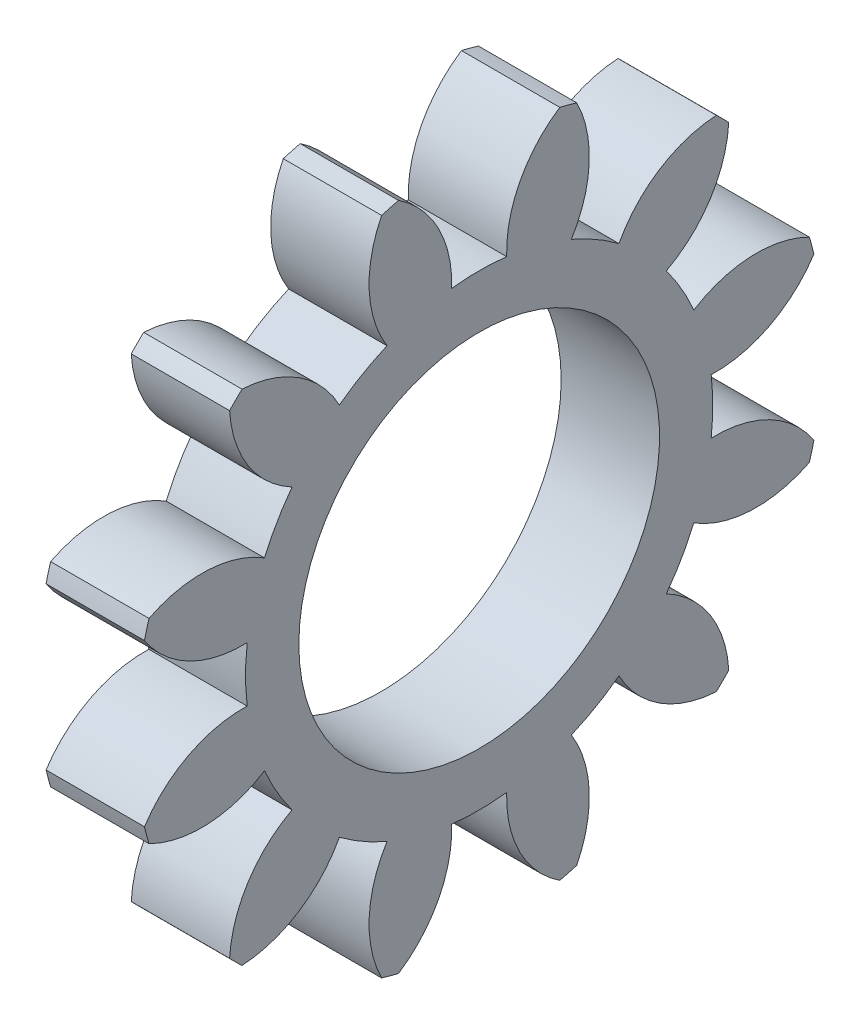
SolidWorks part; units mm, degrees
ref_plane "Plane1" through (0, 0, 0) normal (0, 0, 1) x (1, 0, 0)
ref_plane "Plane2" through (0, 0, 0) normal (0, 1, 0) x (1, 0, 0)
ref_plane "Plane3" through (0, 0, 0) normal (1, 0, 0) x (0, 0, -1)
other "Configuration Table"
sketch "HoldingSke" plane through (0, 0, 0) normal (0, 1, 0) x (1, 0, 0)
  line L0 (0, 0) -> (0.326, -0.0693)
  line L1 (-15, 0) -> (100, 0) construction
  line L2 (0, 0) -> (-2.1039, 2.3779)
  line L3 (0, 0) -> (-11.863, 4.5341)
  line L4 (0, 0) -> (8.4473, 1.7955)
  line L5 (0, 0) -> (-46.8476, -17.4728)
  line L6 (0, 0) -> (-4.9738, -3.3558)
  line L7 (-2.1039, 2.3779) -> (8.6586, 51.2059)
  line L8 (-76.2, 54.61) -> (-72.9, 54.61)
  line L9 (-71.009, 38.7566) -> (-53.1078, 45.2721)
  line L10 (-76.2, 71.12) -> (104.1128, 71.12)
  line L11 (0, 0) -> (-6, 0)
  line L12 (-76.2, 101.6) -> (-76.093, 101.6)
  line L13 (24.9733, 27.94) -> (52.9518, 28.4284)
  line L14 (24.9733, 27.94) -> (24.9743, 27.94)
  line L15 (24.9733, 27.94) -> (100.4006, 29.5858)
  line L16 (-63.627, -3) -> (-12.827, -3)
  circle A0 centre (0, 0) radius 11
  circle A1 centre (0, 0) radius 14.249
  circle A2 centre (0, 0) radius 37.5
  circle A3 centre (0, 0) radius 11
  dimension "MHD" = 28.498
  dimension "Hub_dia" = 75
  dimension "Bore" = 22
  dimension "MBD" = 22
  dimension "Num_teeth" = 12
  dimension "Pitch" = 0.3333
  dimension "Overall_len" = 50
  dimension "Show_teeth" = 12
  dimension "Thickness" = 6
  dimension "OAL" = 50.0001
  dimension "T_dim" = 3.3
  dimension "Ap" = 20
  dimension "H" = 19.05
  dimension "Pitch_radius" = 180.3128
  dimension "Width" = 6
  dimension "Backlash" = 0.107
  dimension "Addendum_fac" = 1
  dimension "Dedendum_fac" = 1.25
  dimension "Clearance_fac" = 0.25
  dimension "Dedendum_add" = 0.001
  dimension "Module" = 3
sketch "BasProSke" plane through (0, 0, 0) normal (0, 1, 0) x (1, 0, 0)
  line L0 (-10, 0) -> (60, 0) construction
  line L1 (0, 0) -> (0, 21)
  line L2 (0, 0) -> (6, 0)
  line L3 (6, 0) -> (6, 21)
  line L4 (6, 21) -> (0, 21)
  dimension "Thickness" = 6
  dimension "Diameter" = 42
revolve "Base-Revolve" add sketch "BasProSke" angle 360 about L0
sketch "TooCutSke" plane through (0, 0, 0) normal (1, 0, 0) x (0, 0, -1)
  line L1 (0, 0) -> (0, 107) construction
  line L2 (0, 0) -> (-2.5365, 17.8204) construction
  line L3 (0, 0) -> (-9.25, 34.5215) construction
  line L4 (-2.5365, 17.8204) -> (-4.625, 17.2608) construction
  arc A0 (1.6769, 14.15) -> (-1.6769, 14.15) centre (0, 0) ccw
  arc A1 (4.9456, 20.4355) -> (-4.9456, 20.4355) centre (0, 0) ccw
  circle A2 centre (0, 0) radius 18 construction
  circle A3 centre (0, 0) radius 16.9145 construction
  arc A4 (-1.6769, 14.15) -> (-4.9456, 20.4355) centre (-8.8725, 14.4006) ccw
  arc A5 (4.9456, 20.4355) -> (1.6769, 14.15) centre (8.8725, 14.4006) ccw
  dimension "Root_dia" = 28.498
  dimension "Overcut_dia" = 42.0508
  dimension "Pitch_dia" = 36
  dimension "Base_dia" = 33.8289
  dimension "Flank_rad" = 7.2
  dimension "Half_ang" = 15
  dimension "Half_CT" = 2.1622
extrude "ToothCut" cut sketch "TooCutSke" along normal through all
fillet "Breaks" [suppressed] radius 0.06
fillet "RootFillets" [suppressed] radius 0.751
pattern_circular "TeethCuts" count 12 every 30 about axis through (-10, 0, 0) along (1, 0, 0) of "ToothCut", "RootFillets", "Breaks"
sketch "HubNeaOneSke" plane through (0, 0, 0) normal (-1, 0, 0) x (0, 0, 1)
  circle A0 centre (0, 0) radius 14.249
  dimension "Diameter" = 28.498
extrude "HubNearOne" [suppressed] add sketch "HubNeaOneSke" along normal blind 44.0001
sketch "HubNeaBotSke" plane through (0, 0, 0) normal (-1, 0, 0) x (0, 0, 1)
  circle A0 centre (0, 0) radius 14.249
  dimension "Diameter" = 28.498
extrude "HubNearBoth" [suppressed] add sketch "HubNeaBotSke" along normal blind 22
ref_plane "FarPln" through (6, 0, 0) normal (1, 0, 0) x (0, 0, -1)
sketch "HubFarSke" plane through (6, 0, 0) normal (1, 0, 0) x (0, 0, -1)
  circle A0 centre (0, 0) radius 14.249
  dimension "Diameter" = 28.498
extrude "HubFar" [suppressed] add sketch "HubFarSke" along normal blind 22
sketch "BorSke" plane through (0, 0, 0) normal (1, 0, 0) x (0, 0, -1)
  circle A0 centre (0, 0) radius 11
  dimension "Diameter" = 22
extrude "Bore" cut sketch "BorSke" along normal mid plane 100.0001
sketch "KeySke" plane through (0, 0, 0) normal (1, 0, 0) x (0, 0, -1)
  line L0 (-4, 0) -> (-4, 14.3)
  line L1 (-4, 14.3) -> (4, 14.3)
  line L2 (4, 14.3) -> (4, 0)
  line L3 (0, 0) -> (0, 34) construction
  line L4 (-4, 0) -> (4, 0)
  dimension "Offset" = 14.3
  dimension "Width" = 8
extrude "Keyway" [suppressed] cut sketch "KeySke" along normal mid plane 100.0001
pattern_circular "Keyway2" [suppressed] count 2 every 90 about axis through (-10, 0, 0) along (1, 0, 0)
equation "' \"Module@HoldingSke\" = 6.35"
equation "' \"Num_teeth@HoldingSke\" = 12"
equation "' \"Ap@HoldingSke\" =  20"
equation "' \"Ap@HoldingSke\" = 20"
equation "' \"Width@HoldingSke\" = 0.5 * 25.4"
equation "' \"Hub_dia@HoldingSke\"= 1 * 25.4"
equation "' \"Hub_dia@HoldingSke\" = 1 * 25.4"
equation "' \"Overall_len@HoldingSke\" = 1.0 * 25.4"
equation "' \"Bore@HoldingSke\" = 0.75 * 25.4"
equation "' \"T_dim@HoldingSke\" = 0.1 * 25.4"
equation "' \"Width@KeySke\" = 0.25 * 25.4"
equation "' \"Show_teeth@HoldingSke\" = 13"
equation "' \"Backlash@HoldingSke\" = 0.009 * 25.4"
equation "' \"Addendum_fac@HoldingSke\" = 1.0"
equation "' \"Dedendum_fac@HoldingSke\" = 1.25"
equation "' \"Dedendum_add@HoldingSke\" = 0.00005 * 25.4"
equation "' \"Clearance_fac@HoldingSke\" = 0.25"
equation "\"Pitch@HoldingSke\" = 1 / \"Module@HoldingSke\""
equation "\"Overcut_dia@TooCutSke\" = (\"Num_teeth@HoldingSke\" + 2 * \"Addendum_fac@HoldingSke\") / \"Pitch@HoldingSke\" + 0.002 * 25.4"
equation "\"Pitch_dia@TooCutSke\" = \"Num_teeth@HoldingSke\" / \"Pitch@HoldingSke\""
equation "\"Base_dia@TooCutSke\" = \"Num_teeth@HoldingSke\" / \"Pitch@HoldingSke\" * cos((\"Ap@HoldingSke\"  * 3.14159265 / 180))"
equation "\"Root_dia@TooCutSke\" = (\"Num_teeth@HoldingSke\" + 2) / \"Pitch@HoldingSke\" - 2 * (\"Addendum_fac@HoldingSke\" + \"Dedendum_fac@HoldingSke\") / \"Pitch@HoldingSke\" - \"Dedendum_add@HoldingSke\" * 2"
equation "\"Half_ang@TooCutSke\" = 180 / \"Num_teeth@HoldingSke\""
equation "\"Half_CT@TooCutSke\" = \"Num_teeth@HoldingSke\" / \"Pitch@HoldingSke\" * sin((3.14159265 / 2 / \"Num_teeth@HoldingSke\")) / 2 - 7 * \"Backlash@HoldingSke\" / 4"
equation "\"Flank_rad@TooCutSke\" = \"Num_teeth@HoldingSke\" / \"Pitch@HoldingSke\" / 5"
equation "\"Radius@RootFillets\" = \"Clearance_fac@HoldingSke\" / \"Pitch@HoldingSke\" + \"Dedendum_add@HoldingSke\""
equation "\"Break_rad@Breaks\" = 0.02 / \"Pitch@HoldingSke\""
equation "\"Thickness@HoldingSke\" = \"Width@HoldingSke\""
equation "\"OAL@HoldingSke\" = \"Thickness@HoldingSke\""
equation "\"MHD@HoldingSke\" = (\"Num_teeth@HoldingSke\" + 2) / \"Pitch@HoldingSke\" - 2 * (\"Addendum_fac@HoldingSke\" + \"Dedendum_fac@HoldingSke\")  / \"Pitch@HoldingSke\" - \"Dedendum_add@HoldingSke\" * 2"
equation "\"MBD@HoldingSke\" = (\"Num_teeth@HoldingSke\" + 2) / \"Pitch@HoldingSke\" - 2 * (\"Addendum_fac@HoldingSke\" + \"Dedendum_fac@HoldingSke\")  / \"Pitch@HoldingSke\" - \"Dedendum_add@HoldingSke\" * 2 - 0.002 * 25.4"
equation "\"MHD@HoldingSke\" = ((sgn( \"MHD@HoldingSke\" - \"Hub_dia@HoldingSke\" )-1)*( \"MHD@HoldingSke\" - \"Hub_dia@HoldingSke\" ))/-2+ \"Hub_dia@HoldingSke\""
equation "\"MBD@HoldingSke\" = ((sgn( \"MBD@HoldingSke\" - \"Bore@HoldingSke\" )-1)*( \"MBD@HoldingSke\" - \"Bore@HoldingSke\" ))/-2+ \"Bore@HoldingSke\""
equation "\"OAL@HoldingSke\" = ((sgn( \"OAL@HoldingSke\" - \"Overall_len@HoldingSke\" )+1)*( \"OAL@HoldingSke\" - \"Overall_len@HoldingSke\" ))/2 + \"Overall_len@HoldingSke\" + 0.000002 * 25.4"
equation "\"Num_teeth@TeethCuts\" = int( \"Show_teeth@HoldingSke\" ) + 1"
equation "\"Num_teeth@TeethCuts\" = ((sgn( \"Num_teeth@TeethCuts\" - \"Num_teeth@HoldingSke\" )-1)*( \"Num_teeth@TeethCuts\" - \"Num_teeth@HoldingSke\" ))/-2+ \"Num_teeth@HoldingSke\""
equation "\"Num_teeth@TeethCuts\" = ((sgn( \"Num_teeth@TeethCuts\" - 2.0)+1)*( \"Num_teeth@TeethCuts\" - 2.0))/2 +2.0"
equation "\"Angle@TeethCuts\" = 360.0 / \"Num_teeth@HoldingSke\""
equation "\"Diameter@BasProSke\" = (\"Num_teeth@HoldingSke\" + 2 * \"Addendum_fac@HoldingSke\") / \"Pitch@HoldingSke\""
equation "\"Thickness@BasProSke\"  = \"Thickness@HoldingSke\""
equation "' \"Fillet_rad@BasProSke\" =  \"Thickness@HoldingSke\" * 0.05"
equation "' \"Fillet_rad@BasProSke\" = \"Thickness@HoldingSke\" * 0.05"
equation "\"MHD@HoldingSke\" = ((sgn( \"MHD@HoldingSke\" - \"Root_dia@TooCutSke\" )-1)*( \"MHD@HoldingSke\" - \"Root_dia@TooCutSke\" ))/-2+ \"Root_dia@TooCutSke\""
equation "\"Diameter@HubNeaOneSke\" = \"MHD@HoldingSke\""
equation "\"Length@HubNearOne\" = \"OAL@HoldingSke\" - \"Thickness@BasProSke\""
equation "\"Diameter@HubNeaBotSke\" = \"MHD@HoldingSke\""
equation "\"Length@HubNearBoth\" = ( \"OAL@HoldingSke\" - \"Thickness@BasProSke\" ) / 2.0"
equation "\"Thickness@FarPln\" = \"Thickness@BasProSke\""
equation "\"Diameter@HubFarSke\" = \"MHD@HoldingSke\""
equation "\"Length@HubFar\" = ( \"OAL@HoldingSke\" - \"Thickness@BasProSke\" ) / 2.0"
equation "\"Diameter@BorSke\" = \"MBD@HoldingSke\""
equation "\"D1@Bore\" = \"OAL@HoldingSke\" * 2.0"
equation "\"D1@Keyway\" = \"OAL@HoldingSke\" * 2.0"
equation "\"Offset@KeySke\" = \"T_dim@HoldingSke\" + \"MBD@HoldingSke\" / 2.0"
